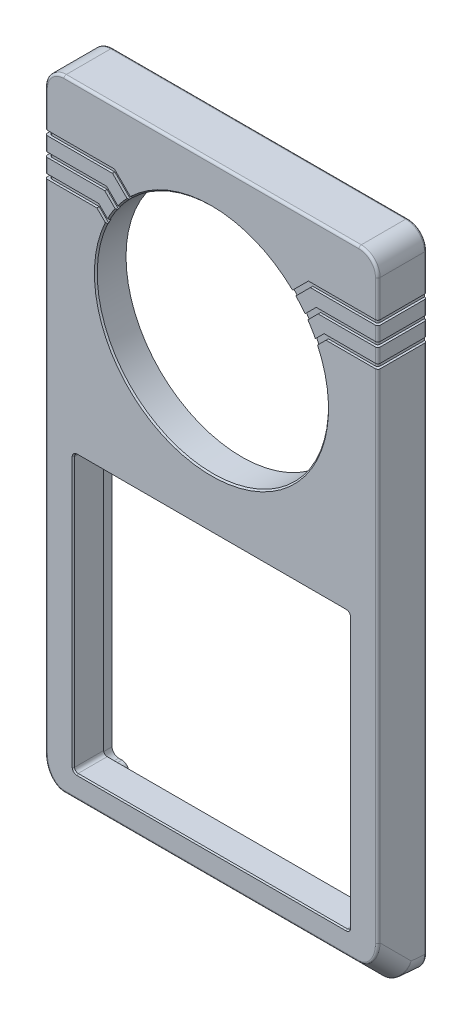
SolidWorks part; units mm, degrees
ref_plane "前视基准面" through (0, 0, 0) normal (0, 0, 1) x (1, 0, 0)
ref_plane "上视基准面" through (0, 0, 0) normal (0, 1, 0) x (1, 0, 0)
ref_plane "右视基准面" through (0, 0, 0) normal (1, 0, 0) x (0, 0, -1)
sketch "草图1" plane through (0, 0, 0) normal (1, 0, 0) x (0, 0, -1)
  line L0 (0, 0) -> (0, 137)
  line L1 (0, 137) -> (-11.4, 137)
  line L2 (-11.4, 137) -> (-11.4, 5.7169)
  line L3 (-11.4, 5.7169) -> (-6.1321, 0.449)
  line L5 (-11.4, 5.7169) -> (6.3075, 5.7169) construction
  line L6 (0, 0) -> (-5.7899, 0) construction
  line L7 (0, 0) -> (-1, 0)
  line L8 (-6.1321, 0.449) -> (-1, 0)
  dimension "D1" = 11.4
  dimension "D2" = 137
  dimension "D3" = 45
  dimension "D4" = 5
  dimension "D5" = 1
  dimension "D6" = 7.45
extrude "凸台-拉伸1" add sketch "草图1" along normal blind 70.5
sketch "草图2" plane through (0, 0, 0) normal (0, 0, -1) x (-1, 0, 0)
  line L0 (0, 0) -> (0, 137) construction
  line L1 (-68.9, 135.4) -> (-1.6, 135.4)
  line L2 (-68.9, 135.4) -> (-68.9, 1.5)
  line L3 (-68.9, 1.5) -> (-1.6, 1.5)
  line L4 (-1.6, 135.4) -> (-1.6, 1.5)
  line L5 (-70.5, 137) -> (0, 137) construction
  line L6 (-70.5, 0) -> (-70.5, 137) construction
  line L7 (-70.5, 0) -> (0, 0) construction
  dimension "D1" = 1.6
  dimension "D2" = 1.6
  dimension "D3" = 1.6
  dimension "D4" = 1.5
extrude "切除-拉伸1" cut sketch "草图2" against normal blind 1 flip side to cut
sketch "草图3" plane through (0, 0, 0) normal (0, 0, -1) x (-1, 0, 0)
  line L0 (-35.25, 159.1782) -> (-35.25, -24.9782) construction
  line L2 (-64.5, 68.75) -> (-6, 68.75)
  line L3 (-64.5, 68.75) -> (-64.5, 10.25)
  line L4 (-64.5, 10.25) -> (-6, 10.25)
  line L5 (-6, 68.75) -> (-6, 10.25)
  line L6 (-64.5, 68.75) -> (-6, 10.25) construction
  line L7 (-64.5, 10.25) -> (-6, 68.75) construction
  line L8 (-70.5, 0) -> (0, 0) construction
  point P2 (-35.25, 39.5)
  dimension "D1" = 58.5
  dimension "D2" = 10.25
extrude "切除-拉伸2" cut sketch "草图3" against normal up to surface (11.4 mm away) up to face at (35.25, 71.3585, 11.4)
sketch "草图5" plane through (0, 0, 0) normal (0, 0, -1) x (-1, 0, 0)
  line L0 (-102.6154, 68.5) -> (30.5586, 68.5) construction
  line L1 (-70.5, 0) -> (0, 0) construction
  line L3 (-70.5, 0) -> (-70.5, 137) construction
  line L4 (0, 0) -> (0, 137) construction
  line L5 (0, 137) -> (-70.5, 137) construction
  circle A0 centre (-65.95, 4.55) radius 0.9
  circle A1 centre (-4.55, 4.55) radius 0.9
  circle A2 centre (-4.55, 132.45) radius 0.9
  circle A3 centre (-65.95, 132.45) radius 0.9
  dimension "D1" = 1.8
  dimension "D2" = 4.55
  dimension "D3" = 4.55
  dimension "D4" = 4.55
  dimension "D5" = 4.55
extrude "切除-拉伸3" cut sketch "草图5" against normal blind 6
sketch "草图6" plane through (0, 0, 0) normal (0, 0, -1) x (-1, 0, 0)
  line L0 (-64.2, 2.7) -> (-6.3, 2.7)
  line L1 (-2.8, 70.55) -> (-2.8, 6.2)
  line L2 (-2.8, 70.55) -> (-2.8, 130.7)
  line L3 (-64.2, 134.2) -> (-6.3, 134.2)
  line L4 (-67.7, 130.7) -> (-67.7, 74.35)
  line L5 (-67.7, 74.35) -> (-67.7, 6.2)
  line L6 (-1.6, 1.5) -> (-1.6, 135.4) construction
  line L7 (-68.9, 1.5) -> (-1.6, 1.5) construction
  line L8 (-68.9, 135.4) -> (-68.9, 1.5) construction
  line L9 (-1.6, 135.4) -> (-68.9, 135.4) construction
  line L10 (-64.2, 2.7) -> (-64.2, 6.2)
  line L11 (-64.2, 6.2) -> (-67.7, 6.2)
  line L12 (-6.3, 2.7) -> (-6.3, 6.2)
  line L13 (-6.3, 6.2) -> (-2.8, 6.2)
  line L17 (-6.3, 134.2) -> (-6.3, 130.7)
  line L18 (-6.3, 130.7) -> (-2.8, 130.7)
  line L19 (-67.7, 130.7) -> (-64.2, 130.7)
  line L20 (-64.2, 130.7) -> (-64.2, 134.2)
  dimension "D1" = 1.2
  dimension "D2" = 1.2
  dimension "D3" = 1.2
  dimension "D4" = 1.2
  dimension "D5" = 4.7
extrude "切除-拉伸4" cut sketch "草图6" against normal blind 5
fillet "圆角1" radius 1.4 8 edges at (67.7, 6.2, 2.5) (64.2, 2.7, 2.5) (2.8, 6.2, 2.5) (6.3, 2.7, 2.5) (2.8, 130.7, 2.5) (6.3, 134.2, 2.5) (67.7, 130.7, 2.5) (64.2, 134.2, 2.5)
fillet "圆角2" radius 1.4 4 edges at (6.3, 6.2, 2.5) (64.2, 6.2, 2.5) (6.3, 130.7, 2.5) (64.2, 130.7, 2.5)
fillet "圆角4" radius 4 6 edges at (70.5, 3.083, 8.766) (70.5, 0.2245, 3.566) (0, 3.083, 8.766) (0, 0.2245, 3.566) (0, 137, 6.2) (70.5, 137, 6.2)
fillet "圆角7" radius 2.2 4 edges at (1.6, 1.5, 0.5) (68.9, 1.5, 0.5) (1.6, 135.4, 0.5) (68.9, 135.4, 0.5)
fillet "圆角8" radius 0.5 27 edges at (69.3284, 1.5789, 5.6052) (1.1716, 1.5789, 5.6052) (69.3284, 135.8284, 11.4) (70.5, 72.1869, 11.4) (69.3284, 7.3738, 11.4) (35.25, 5.7169, 11.4) (1.1716, 7.3738, 11.4) (0, 72.1869, 11.4) (1.1716, 135.8284, 11.4) (1.1716, 135.8284, 1) (0, 68.5076, 1) (1.1716, 1.176, 1) (35.25, 0, 1) (69.3284, 1.176, 1) (70.5, 68.5076, 1) (69.3284, 135.8284, 1) (2.2444, 134.7556, 0) (1.6, 68.45, 0) (2.2444, 2.1444, 0) (35.25, 1.5, 0) (68.2556, 2.1444, 0) (68.9, 68.45, 0) (68.2556, 134.7556, 0) (35.25, 0.449, 6.1321) (35.25, 137, 11.4) (35.25, 137, 1) (35.25, 135.4, 0)
fillet "圆角9" radius 0.75 4 edges at (64.5, 68.75, 8.2) (6, 68.75, 8.2) (6, 10.25, 8.2) (64.5, 10.25, 8.2)
chamfer "倒角1" distance 0.25 angle 45 8 edges at (35.25, 10.25, 11.4) (64.5, 39.5, 11.4) (6, 39.5, 11.4) (35.25, 68.75, 11.4) (64.2803, 10.4697, 11.4) (6.2197, 10.4697, 11.4) (64.2803, 68.5303, 11.4) (6.2197, 68.5303, 11.4)
sketch "草图8" plane through (0, 0, 11.4) normal (0, 0, 1) x (1, 0, 0)
  line L0 (35.25, 149.8206) -> (35.25, 49.657) construction
  line L1 (8.2018, 104) -> (91.4946, 104) construction
  line L2 (4, 137) -> (66.5, 137) construction
  line L5 (6.75, 69) -> (63.75, 69) construction
  line L6 (66.5, 136.5) -> (4, 136.5) construction
  circle A0 centre (35.25, 104) radius 24.5
  point P6 (35.25, 104)
  point P7 (35.25, 136.5)
  point P15 (35.25, 69)
  dimension "D1" = 49
  dimension "D2" = 33
extrude "切除-拉伸5" cut sketch "草图8" against normal up to next
chamfer "倒角2" distance 0.3 angle 45 1 edges at (59.75, 104, 11.4)
sketch "草图9" plane through (0, 0, 5) normal (0, 0, -1) x (-1, 0, 0)
  line L0 (-67.7, 129.3) -> (-67.7, 7.6) construction
  line L1 (-4.2, 130.7) -> (-4.9, 130.7) construction
  line L2 (-6.3, 132.1) -> (-6.3, 132.8) construction
  line L3 (-7.7, 134.2) -> (-62.8, 134.2) construction
  line L4 (-64.2, 132.8) -> (-64.2, 132.1) construction
  line L5 (-65.6, 130.7) -> (-66.3, 130.7) construction
  line L6 (-2.8, 7.6) -> (-2.8, 129.3) construction
  line L7 (-4.2, 130.7) -> (-4.9, 130.7)
  line L8 (-6.3, 132.1) -> (-6.3, 132.8)
  line L9 (-7.7, 134.2) -> (-62.8, 134.2)
  line L10 (-64.2, 132.8) -> (-64.2, 132.1)
  line L11 (-65.6, 130.7) -> (-66.3, 130.7)
  line L12 (-2.8, 7.6) -> (-2.8, 129.3) construction
  line L13 (-67.7, 129.3) -> (-67.7, 7.6) construction
  line L14 (-67.7, 72.5038) -> (-2.8, 72.5038)
  line L15 (-67.7, 72.5038) -> (-67.7, 129.3)
  line L16 (-2.8, 129.3) -> (-2.8, 72.5038)
  circle A0 centre (-35.25, 104) radius 24.5 construction
  circle A1 centre (-35.25, 104) radius 24.5 construction
  circle A2 centre (-35.25, 104) radius 26
  arc A3 (-2.8, 129.3) -> (-4.2, 130.7) centre (-4.2, 129.3) ccw construction
  arc A4 (-6.3, 132.1) -> (-4.9, 130.7) centre (-4.9, 132.1) ccw construction
  arc A5 (-6.3, 132.8) -> (-7.7, 134.2) centre (-7.7, 132.8) ccw construction
  arc A6 (-62.8, 134.2) -> (-64.2, 132.8) centre (-62.8, 132.8) ccw construction
  arc A7 (-65.6, 130.7) -> (-64.2, 132.1) centre (-65.6, 132.1) ccw construction
  arc A8 (-66.3, 130.7) -> (-67.7, 129.3) centre (-66.3, 129.3) ccw construction
  arc A9 (-2.8, 129.3) -> (-4.2, 130.7) centre (-4.2, 129.3) ccw
  arc A10 (-6.3, 132.1) -> (-4.9, 130.7) centre (-4.9, 132.1) ccw
  arc A11 (-6.3, 132.8) -> (-7.7, 134.2) centre (-7.7, 132.8) ccw
  arc A12 (-62.8, 134.2) -> (-64.2, 132.8) centre (-62.8, 132.8) ccw
  arc A13 (-65.6, 130.7) -> (-64.2, 132.1) centre (-65.6, 132.1) ccw
  arc A14 (-66.3, 130.7) -> (-67.7, 129.3) centre (-66.3, 129.3) ccw
  dimension "D1" = 52
extrude "切除-拉伸6" cut sketch "草图9" against normal offset from surface (4.4 mm away) 2 up to face at (35.25, 128.8, 11.4)
sketch "草图10" plane through (0, 0, 9.4) normal (0, 0, -1) x (-1, 0, 0)
  line L0 (-67.7, 72.5038) -> (-2.8, 72.5038) construction
  line L1 (-67.7, 72.5038) -> (-66.2, 72.5038)
  line L2 (-67.7, 72.5038) -> (-67.7, 74.0038)
  line L3 (-67.7, 74.0038) -> (-66.2, 74.0038)
  line L4 (-66.2, 72.5038) -> (-66.2, 74.0038)
  line L5 (-67.7, 129.3) -> (-67.7, 7.6) construction
  line L6 (-2.8, 7.6) -> (-2.8, 129.3) construction
  line L7 (-2.8, 72.5038) -> (-4.3, 72.5038)
  line L8 (-2.8, 72.5038) -> (-2.8, 74.0038)
  line L9 (-2.8, 74.0038) -> (-4.3, 74.0038)
  line L10 (-4.3, 72.5038) -> (-4.3, 74.0038)
  dimension "D1" = 1.5
extrude "凸台-拉伸2" add sketch "草图10" along normal offset from surface (5.6 mm away) 1.2 up to face at (35.25, 14.8306, 5) offset beyond the face yes
sketch "草图11" plane through (0, 0, 11.4) normal (0, 0, 1) x (1, 0, 0)
  line L0 (35.25, 104) -> (75.4011, 144.1511) construction
  line L1 (72.0311, 124.75) -> (56, 124.75)
  line L2 (56, 124.75) -> (51.6018, 120.3518)
  line L3 (74.3218, 120.75) -> (57.6569, 120.75)
  line L4 (-4.6191, 120.75) -> (77.4805, 120.75) construction
  line L5 (-3.8656, 124.75) -> (77.4805, 124.75) construction
  line L6 (-3.8656, 116.75) -> (77.4805, 116.75) construction
  line L7 (-1.4055, 124.75) -> (14.5, 124.75)
  line L8 (14.5, 124.75) -> (18.3556, 120.8944)
  line L9 (57.6569, 120.75) -> (50.2559, 113.349)
  line L10 (-1.7601, 120.75) -> (12.8431, 120.75)
  line L11 (12.8431, 120.75) -> (15.9307, 117.6624)
  line L12 (-2.0294, 116.75) -> (11.1863, 116.75)
  line L13 (76.8305, 116.75) -> (59.3137, 116.75)
  line L14 (11.1863, 116.75) -> (13.5248, 114.4115)
  line L15 (-13.7502, 153.0002) -> (61.9834, 77.2666) construction
  line L16 (59.3137, 116.75) -> (53.2424, 110.6787)
  arc A2 (35.25, 102.6) -> (35.25, 105.4) centre (35.25, 104) ccw construction
  dimension "D1" = 4
  dimension "D2" = 45
  dimension "D3" = 4
  dimension "D4" = 4
  dimension "D5" = 4
  dimension "D6" = 4
extrude "切除-拉伸-薄壁2" cut sketch "草图11" against normal blind 0.5 thin thin type mid plane wall 1
sketch "草图12" plane through (0, 0, 0) normal (-1, 0, 0) x (0, 0, 1)
  line L0 (-2.208, 120.75) -> (13.2309, 120.75) construction
  line L1 (12.4755, 124.75) -> (-1.6429, 124.75)
  line L2 (12.4755, 116.75) -> (-2.0654, 116.75)
  line L3 (12.4755, 120.75) -> (-1.4428, 120.75)
  dimension "D1" = 4
  dimension "D2" = 4
extrude "切除-拉伸-薄壁3" cut sketch "草图12" against normal blind 0.5 thin
sketch "草图13" plane through (70.5, 0, 0) normal (1, 0, 0) x (0, 0, -1)
  line L0 (-12.0491, 120.75) -> (3.0323, 120.75) construction
  line L1 (-12.6039, 124.75) -> (0.3998, 124.75)
  line L2 (-12.6039, 116.75) -> (0.8956, 116.75)
  line L3 (-11.7204, 120.75) -> (-0.3515, 120.75)
  dimension "D1" = 4
extrude "切除-拉伸-薄壁4" cut sketch "草图13" against normal blind 0.5 thin
fillet "圆角10" radius 0.5 6 edges at (70, 116.75, 10.9) (70, 120.75, 10.9) (70, 124.75, 10.9) (0.5, 116.75, 10.9) (0.5, 120.75, 10.9) (0.5, 124.75, 10.9)
